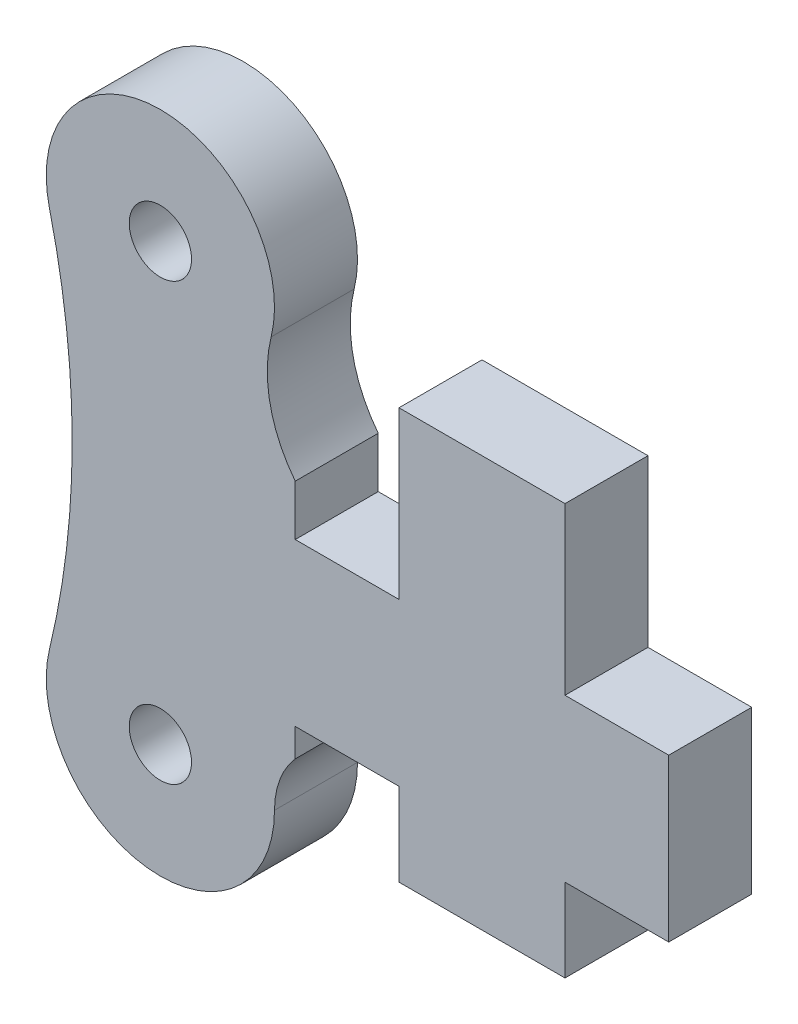
SolidWorks part; units mm, degrees
ref_plane "Front Plane" through (0, 0, 0) normal (0, 0, 1) x (1, 0, 0)
ref_plane "Top Plane" through (0, 0, 0) normal (0, 1, 0) x (1, 0, 0)
ref_plane "Right Plane" through (0, 0, 0) normal (1, 0, 0) x (0, 0, -1)
sketch "Sketch1" plane through (0, 0, 0) normal (0, 0, 1) x (1, 0, 0)
  line L0 (0, 0) -> (0, -21) construction
  line L1 (11.5, -9.2) -> (24.5, -9.2)
  line L2 (9.5, -17) -> (24.5, -17)
  line L3 (24.5, -9.2) -> (24.5, -17)
  line L5 (19.5, -9.2) -> (11.5, -9.2)
  line L6 (19.5, -9.2) -> (19.5, -1.2)
  line L7 (19.5, -1.2) -> (11.5, -1.2)
  line L8 (11.5, -9.2) -> (11.5, -1.2)
  line L9 (11.5, -17) -> (19.5, -17)
  line L10 (11.5, -17) -> (11.5, -21)
  line L11 (11.5, -21) -> (19.5, -21)
  line L12 (19.5, -17) -> (19.5, -21)
  circle A0 centre (0, 0) radius 1.5
  circle A1 centre (0, 0) radius 5.5
  circle A2 centre (0, -21) radius 1.5
  circle A3 centre (0, -21) radius 5.5
  arc A4 (-5.3463, -1.2912) -> (-5.3463, -19.7088) centre (-43.475, -10.5) cw
  arc A5 (5.3383, -1.3238) -> (11.5, -9.2) centre (11.5, -2.8517) ccw
  arc A6 (5.5, -21) -> (9.5, -17) centre (9.5, -21) cw
  point P7 (-4.25, -10.5)
  point P27 (15.5, -21)
  point P28 (15.5, -1.2)
  point P29 (7.3287, -9)
  point P30 (0, 0)
  dimension "D1" = 4
  dimension "D2" = 3
  dimension "D4" = 0
  dimension "D7" = 4.25
  dimension "D8" = 0
  dimension "D3" = 21
  dimension "D5" = 7.8
  dimension "D6" = 4
  dimension "D9" = 15
  dimension "D10" = 8
  dimension "D11" = 8
  dimension "D12" = 4
  dimension "D13" = 5
extrude "Boss-Extrude1" add sketch "Sketch1" along normal blind 4
sketch "Sketch2" plane through (0, 0, 4) normal (0, 0, 1) x (1, 0, 0)
  line L1 (11.5, -9.2) -> (6.5, -9.2)
  line L2 (11.5, -9.2) -> (11.5, -4.2)
  line L3 (11.5, -4.2) -> (6.5, -4.2)
  line L4 (6.5, -9.2) -> (6.5, -4.2)
  line L5 (11.5, -17) -> (6.5, -17)
  line L6 (11.5, -17) -> (11.5, -22)
  line L7 (11.5, -22) -> (6.5, -22)
  line L8 (6.5, -17) -> (6.5, -22)
  dimension "D1" = 5
  dimension "D2" = 5
extrude "Cut-Extrude1" cut sketch "Sketch2" against normal blind 4
